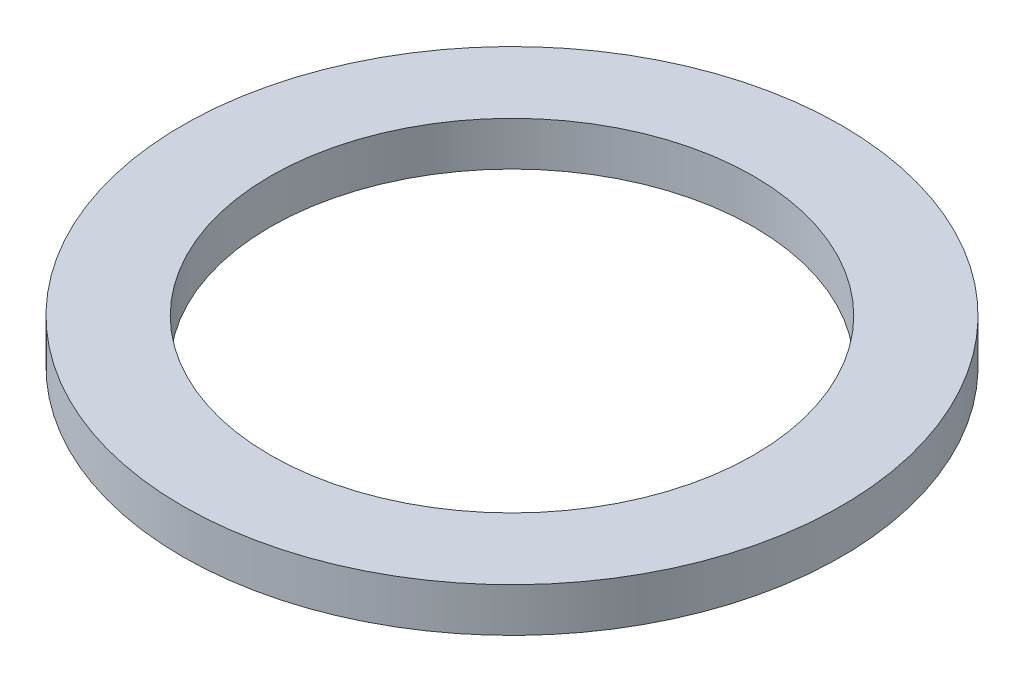
SolidWorks part; units mm, degrees
ref_plane "Front Plane" through (0, 0, 0) normal (0, 0, 1) x (1, 0, 0)
ref_plane "Top Plane" through (0, 0, 0) normal (0, 1, 0) x (1, 0, 0)
ref_plane "Right Plane" through (0, 0, 0) normal (1, 0, 0) x (0, 0, -1)
sketch "Sketch1" plane through (0, 0, 0) normal (0, 1, 0) x (1, 0, 0)
  circle A0 centre (0, 0) radius 3.75
  circle A1 centre (0, 0) radius 2.75
  dimension "D1" = 5.5
  dimension "D2" = 7.5
extrude "Boss-Extrude1" add sketch "Sketch1" along normal blind 0.5
